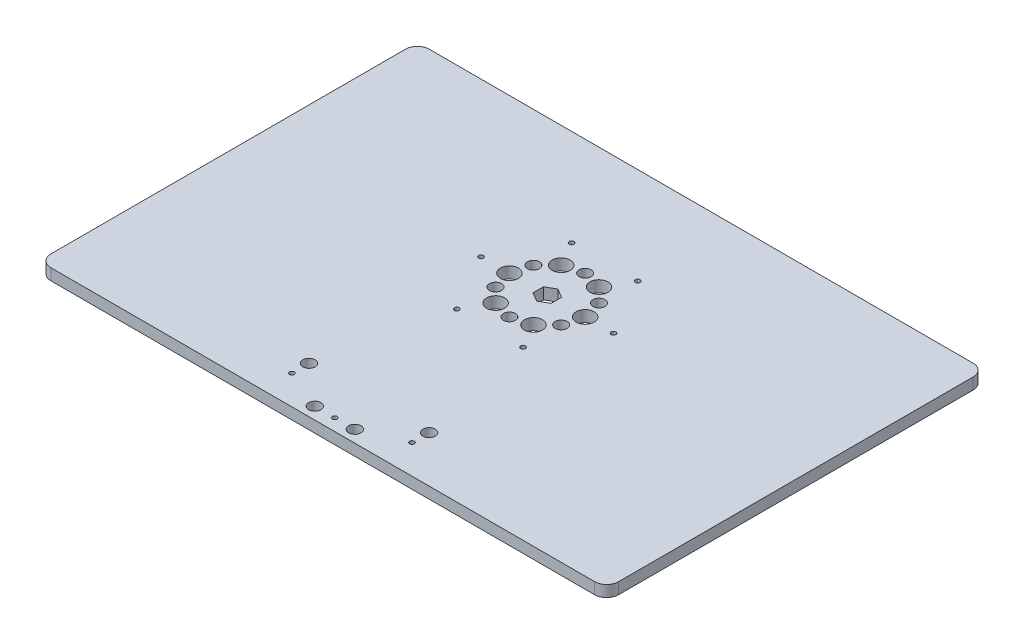
SolidWorks part; units mm, degrees
material "Balsa"
ref_plane "Front" through (0, 0, 0) normal (0, 0, 1) x (1, 0, 0)
ref_plane "Top" through (0, 0, 0) normal (0, 1, 0) x (1, 0, 0)
ref_plane "Right" through (0, 0, 0) normal (1, 0, 0) x (0, 0, -1)
sketch "Sketch1" plane through (0, 0, 0) normal (0, 1, 0) x (1, 0, 0)
  line L0 (150, 0) -> (150, 200) construction
  line L1 (0, 0) -> (300, 0)
  line L2 (0, 0) -> (0, 200)
  line L3 (0, 200) -> (300, 200)
  line L4 (300, 0) -> (300, 200)
  dimension "D2" = 300
  dimension "D6" = 200
extrude "Boss-Extrude1" add sketch "Sketch1" along normal blind 6
sketch "Sketch6" plane through (0, 6, 0) normal (0, 1, 0) x (1, 0, 0)
  line L0 (150, 118.651) -> (150, 0) construction
  line L1 (0, 0) -> (300, 0) construction
  circle A0 centre (150, 118.651) radius 2.5
  dimension "D1" = 5
  dimension "D2" = 118.651
extrude "Cut-Extrude2" cut sketch "Sketch6" against normal through all
fillet "Fillet1" radius 6.35 4 edges at (0, 3, 0) (300, 3, 0) (300, 3, -200) (0, 3, -200)
sketch "Sketch13" plane through (0, 6, 5.8) normal (0, 1, 0) x (1, 0, 0)
  line L0 (150, 5.8) -> (150, 205.8) construction
  line L1 (6.35, 5.8) -> (293.65, 5.8) construction
  line L2 (293.65, 205.8) -> (6.35, 205.8) construction
  line L3 (0, 199.45) -> (0, 12.15) construction
  line L4 (6.35, 99.4498) -> (6.35, 12.15) construction
  line L5 (6.35, 12.15) -> (82.55, 12.15) construction
  line L6 (82.55, 12.15) -> (82.55, 1.2299) construction
  line L22 (293.65, 12.15) -> (217.45, 12.15) construction
  line L23 (293.65, 99.4498) -> (293.65, 12.15) construction
  line L26 (150, 199.45) -> (78.175, 199.45) construction
  line L27 (78.175, 199.45) -> (6.35, 199.45) construction
  circle A0 centre (6.35, 199.45) radius 1.25
  circle A1 centre (78.175, 199.45) radius 1.25
  circle A2 centre (221.825, 199.45) radius 1.25
  circle A3 centre (293.65, 199.45) radius 1.25
  circle A4 centre (293.65, 99.4498) radius 1.25
  circle A5 centre (293.65, 12.15) radius 1.25
  circle A6 centre (217.45, 12.15) radius 1.25
  circle A7 centre (82.55, 12.15) radius 1.25
  circle A8 centre (6.35, 12.15) radius 1.25
  circle A9 centre (6.35, 99.4498) radius 1.25
  point P0 (6.35, 99.4498)
  point P1 (6.35, 12.15)
  point P10 (82.55, 12.15)
  point P71 (293.65, 99.4498)
  point P75 (217.45, 12.15)
  point P77 (293.65, 12.15)
  point P85 (6.35, 199.45)
  point P87 (78.175, 199.45)
  point P101 (221.825, 199.45)
  point P102 (293.65, 199.45)
  dimension "D2" = 76.2
  dimension "D7" = 2.5
  dimension "D1" = 6.35
  dimension "D3" = 6.35
  dimension "D4" = 6.35
  dimension "D5" = 6.35
  dimension "D6" = 87.2998
sketch "Sketch2" plane through (0, 6, 0) normal (0, 1, 0) x (1, 0, 0)
  line L0 (150, 49.9999) -> (150, 0) construction
  line L1 (6.35, 0) -> (293.65, 0) construction
  line L2 (0, 49.9999) -> (300, 49.9999) construction
  line L3 (0, 193.65) -> (0, 6.35) construction
  line L4 (150, 49.9999) -> (150, 99.9998) construction
  line L5 (50.8, 75.3999) -> (50.8, 49.9999) construction
  line L6 (300, 6.35) -> (300, 193.65) construction
  line L7 (0, 193.65) -> (0, 6.35) construction
  line L8 (293.65, 200) -> (6.35, 200) construction
  line L9 (150, 99.9998) -> (0, 99.9998) construction
  line L10 (0, 193.65) -> (0, 6.35) construction
  circle A0 centre (6.35, 174.6) radius 1.5
  circle A1 centre (6.35, 49.9999) radius 1.5
  circle A2 centre (249.2, 75.3999) radius 1.5 construction
  circle A3 centre (50.8, 75.3999) radius 1.5 construction
  circle A4 centre (293.65, 49.9999) radius 1.5
  circle A5 centre (50.8, 24.5999) radius 1.5 construction
  circle A6 centre (249.2, 24.5999) radius 1.5 construction
  circle A7 centre (25.4, 193.65) radius 1.5 construction
  circle A9 centre (293.65, 174.6) radius 1.5
  dimension "D1" = 3
  dimension "D8" = 25.4
  dimension "D9" = 25.4
  dimension "D2" = 6.35
  dimension "D3" = 25.4
  dimension "D4" = 50.8
  dimension "D5" = 99.9998
  dimension "D6" = 6.35
  dimension "D7" = 6.35
extrude "Cut-Extrude1" [suppressed] cut sketch "Sketch2" against normal through all
extrude "M3-tap" [suppressed] cut sketch "Sketch13" against normal through all
sketch "Sketch16" plane through (0, 6, -5.8) normal (0, -1, 0) x (1, 0, 0)
  line L0 (150, -112.851) -> (150, 0) construction
  line L3 (150, -25.001) -> (181.75, -25.001) construction
  line L4 (181.75, -25.001) -> (181.75, -0.551) construction
  line L6 (118.25, -0.551) -> (139.4167, -0.551) construction
  line L7 (139.4167, -0.551) -> (160.5833, -0.551) construction
  line L8 (160.5833, -0.551) -> (181.75, -0.551) construction
  circle A0 centre (150, -112.851) radius 80 construction
  circle A1 centre (150, -112.851) radius 2.5 construction
  circle A2 centre (150, -25.001) radius 7.85 construction
  circle A3 centre (150, -25.001) radius 6.35 construction
  circle A4 centre (118.25, -18.651) radius 3.25
  circle A5 centre (118.25, -0.551) radius 3.25 construction
  circle A6 centre (139.4167, -0.551) radius 3.25
  circle A7 centre (160.5833, -0.551) radius 3.25
  circle A8 centre (181.75, -0.551) radius 3.25 construction
  circle A9 centre (181.75, -18.651) radius 3.25
  point P0 (181.75, -0.551)
  point P28 (181.75, -18.651)
  point P32 (118.25, -18.651)
  point P33 (118.25, -0.551)
  point P34 (139.4167, -0.551)
  point P36 (160.5833, -0.551)
  dimension "D1" = 160
  dimension "D2" = 1.5
  dimension "D3" = 12.7
  dimension "D7" = 6.5
  dimension "D4" = 31.75
  dimension "D5" = 24.45
  dimension "D6" = 18.1
extrude "M5-tap2" cut sketch "Sketch16" along normal through all
sketch "Sketch17" plane through (0, 6, 0) normal (0, 1, 0) x (1, 0, 0)
  line L0 (150, 118.651) -> (185, 118.651) construction
  line L1 (132.5, 148.9619) -> (150, 118.651) construction
  line L2 (150, 118.651) -> (167.5, 148.9619) construction
  line L3 (150, 118.651) -> (150, 138.651) construction
  circle A0 centre (185, 118.651) radius 1.25
  circle A1 centre (167.5, 88.3401) radius 1.25
  circle A2 centre (132.5, 88.3401) radius 1.25
  circle A3 centre (115, 118.651) radius 1.25
  circle A4 centre (132.5, 148.9619) radius 1.25
  circle A5 centre (167.5, 148.9619) radius 1.25
  circle A6 centre (150, 138.651) radius 3.175
  circle A7 centre (167.3205, 128.651) radius 3.175
  circle A8 centre (167.3205, 108.651) radius 3.175
  circle A9 centre (150, 98.651) radius 3.175
  circle A10 centre (132.6795, 108.651) radius 3.175
  circle A11 centre (132.6795, 128.651) radius 3.175
  circle A12 centre (160, 135.9715) radius 4.7625
  circle A13 centre (170, 118.651) radius 4.7625
  circle A14 centre (160, 101.3305) radius 4.7625
  circle A15 centre (140, 101.3305) radius 4.7625
  circle A16 centre (130, 118.651) radius 4.7625
  circle A17 centre (140, 135.9715) radius 4.7625
  point P28 (150, 118.651)
  point P30 (132.5, 97.2214)
  point P31 (0, 0)
  point P41 (150, 118.651)
  dimension "D1" = 2.5
  dimension "D3" = 6.35
  dimension "D6" = 20
  dimension "D7" = 9.525
  dimension "D2" = 35
  dimension "D4" = 20
  dimension "D5" = 6
  dimension "D8" = 6
extrude "M3_counterbore" cut sketch "Sketch17" against normal through all
sketch "Sketch18" plane through (0, 6, 0) normal (0, 1, 0) x (1, 0, 0)
  line L0 (150, 118.651) -> (154.8, 118.651) construction
  line L1 (154.8, 121.4223) -> (154.8, 115.8797)
  line L2 (154.8, 115.8797) -> (150, 113.1085)
  line L3 (150, 113.1085) -> (145.2, 115.8797)
  line L4 (145.2, 115.8797) -> (145.2, 121.4223)
  line L5 (145.2, 121.4223) -> (150, 124.1936)
  line L6 (150, 124.1936) -> (154.8, 121.4223)
  line L7 (150, 118.651) -> (145.2, 118.651) construction
  dimension "D2" = 9.6
  dimension "D1" = 6
extrude "Cut-Extrude6" cut sketch "Sketch18" against normal through all
sketch "Sketch19" plane through (0, 6, 0) normal (0, 1, 0) x (1, 0, 0)
  line L0 (118.25, 24.451) -> (118.25, 6.351) construction
  line L1 (181.75, 24.451) -> (181.75, 6.351) construction
  line L2 (181.75, 6.351) -> (118.25, 6.351) construction
  circle A0 centre (139.4167, 6.351) radius 3.25 construction
  circle A1 centre (139.4167, 6.351) radius 3.25 construction
  circle A2 centre (118.25, 15.401) radius 1.25
  circle A3 centre (150, 6.351) radius 1.25
  circle A4 centre (181.75, 15.401) radius 1.25
  dimension "D1" = 2.5
  dimension "D2" = 2.5
  dimension "D3" = 2.5
extrude "Cut-Extrude7" cut sketch "Sketch19" against normal through all
